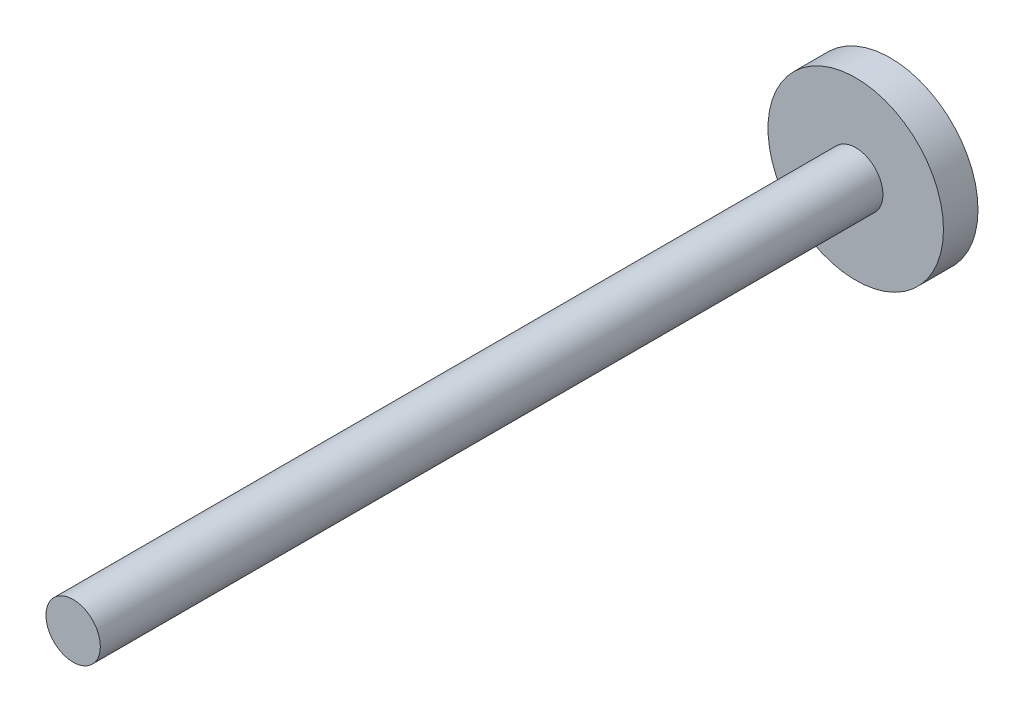
SolidWorks part; units mm, degrees
ref_plane "Front Plane" through (0, 0, 0) normal (0, 0, 1) x (1, 0, 0)
ref_plane "Top Plane" through (0, 0, 0) normal (0, 1, 0) x (1, 0, 0)
ref_plane "Right Plane" through (0, 0, 0) normal (1, 0, 0) x (0, 0, -1)
sketch "Sketch1" plane through (0, 0, 0) normal (0, 0, 1) x (1, 0, 0)
  circle A0 centre (0, 0) radius 12.7
  dimension "D1" = 25.4
extrude "Boss-Extrude1" add sketch "Sketch1" along normal blind 5
sketch "Sketch2" plane through (0, 0, 5) normal (0, 0, 1) x (1, 0, 0)
  circle A0 centre (0, 0) radius 3.937
  dimension "D1" = 7.874
extrude "Boss-Extrude3" add sketch "Sketch2" along normal blind 113.284 contours A0
